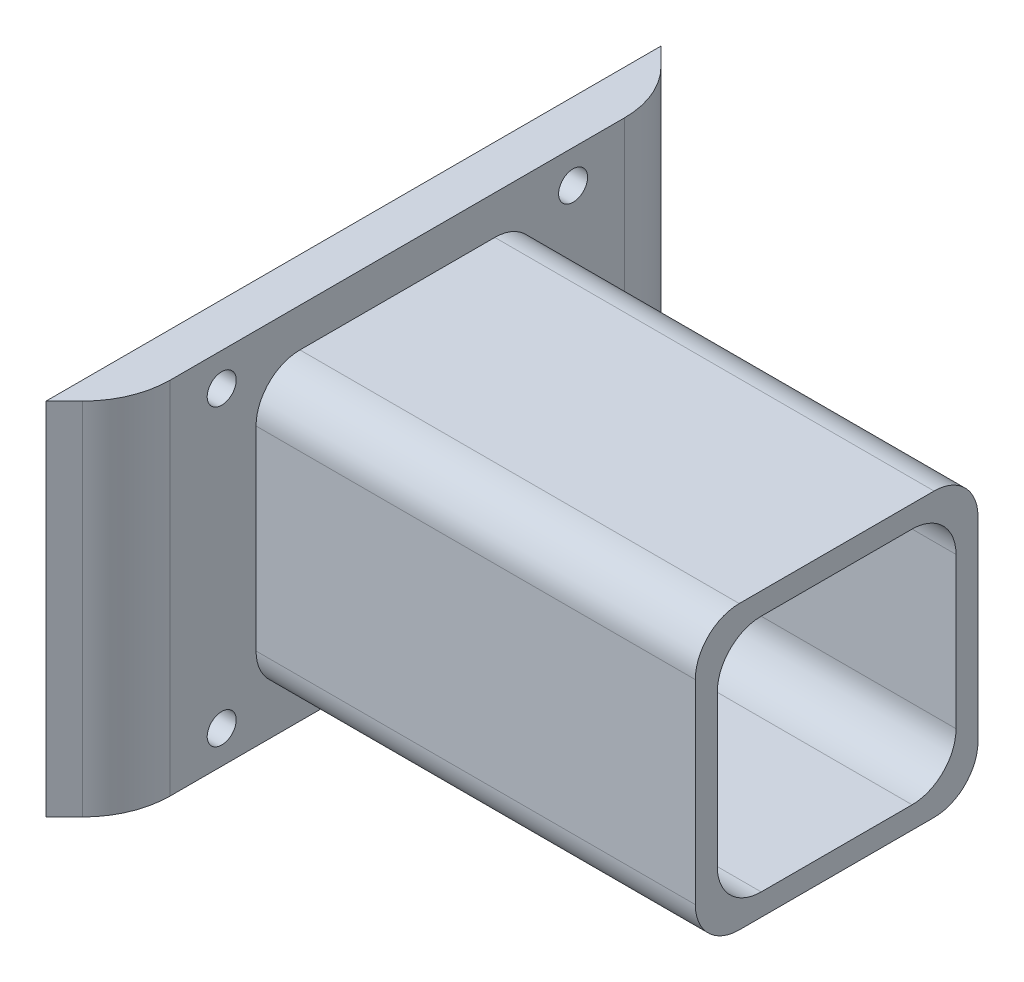
SolidWorks part; units mm, degrees
material "6061 Alloy"
ref_plane "Front Plane" through (0, 0, 0) normal (0, 0, 1) x (1, 0, 0)
ref_plane "Top Plane" through (0, 0, 0) normal (0, 1, 0) x (1, 0, 0)
ref_plane "Right Plane" through (0, 0, 0) normal (1, 0, 0) x (0, 0, -1)
sketch "Sketch1" plane through (0, 0, 0) normal (1, 0, 0) x (0, 0, -1)
  line L1 (-60, -41) -> (60, -41)
  line L2 (-60, -41) -> (-60, 41)
  line L3 (-60, 41) -> (60, 41)
  line L4 (60, -41) -> (60, 41)
  line L5 (-60, -41) -> (60, 41) construction
  line L6 (-60, 41) -> (60, -41) construction
  point P0 (0, 0)
  dimension "D1" = 82
  dimension "D2" = 120
extrude "Boss-Extrude1" add sketch "Sketch1" along normal blind 10
sketch "Sketch6" plane through (0, 41, 0) normal (0, 1, 0) x (1, 0, 0)
  line L0 (0, 60) -> (0, 70)
  line L1 (0, 70) -> (10, 60)
  line L2 (10, 60) -> (0, 60)
  line L3 (0, -60) -> (0, -70)
  line L4 (0, -70) -> (10, -60)
  line L5 (10, -60) -> (0, -60)
  dimension "D1" = 10
  dimension "D2" = 10
extrude "Boss-Extrude4" add sketch "Sketch6" against normal up to surface (82 mm away) up to face at (5, -41, 0)
fillet "Fillet2" radius 20 2 edges at (10, 0, -60) (10, 0, 60)
sketch "Sketch7" plane through (10, 0, 0) normal (1, 0, 0) x (0, 0, -1)
  line L1 (-17.18, -27.18) -> (17.18, -27.18)
  line L2 (-27.18, -17.18) -> (-27.18, 17.18)
  line L3 (-17.18, 27.18) -> (17.18, 27.18)
  line L4 (27.18, -17.18) -> (27.18, 17.18)
  line L5 (-27.18, -27.18) -> (27.18, 27.18) construction
  line L6 (-27.18, 27.18) -> (27.18, -27.18) construction
  line L7 (-22.18, -32.18) -> (22.18, -32.18)
  line L8 (-32.18, -22.18) -> (-32.18, 22.18)
  line L9 (-22.18, 32.18) -> (22.18, 32.18)
  line L10 (32.18, -22.18) -> (32.18, 22.18)
  line L11 (-32.18, -32.18) -> (32.18, 32.18) construction
  line L12 (-32.18, 32.18) -> (32.18, -32.18) construction
  arc A0 (22.18, -32.18) -> (32.18, -22.18) centre (22.18, -22.18) ccw
  arc A1 (22.18, 32.18) -> (32.18, 22.18) centre (22.18, 22.18) cw
  arc A2 (-32.18, 22.18) -> (-22.18, 32.18) centre (-22.18, 22.18) cw
  arc A3 (-22.18, -32.18) -> (-32.18, -22.18) centre (-22.18, -22.18) cw
  arc A4 (-17.18, -27.18) -> (-27.18, -17.18) centre (-17.18, -17.18) cw
  arc A5 (17.18, -27.18) -> (27.18, -17.18) centre (17.18, -17.18) ccw
  arc A6 (17.18, 27.18) -> (27.18, 17.18) centre (17.18, 17.18) cw
  arc A7 (-27.18, 17.18) -> (-17.18, 27.18) centre (-17.18, 17.18) cw
  point P0 (0, 0)
  point P6 (0, 0)
  dimension "D5" = 10
  dimension "D1" = 54.36
  dimension "D2" = 54.36
  dimension "D3" = 5
  dimension "D4" = 5
extrude "Boss-Extrude5" add sketch "Sketch7" along normal blind 100
hole_wizard "M6 Clearance Hole1" positions "Sketch8" profile "Sketch9" hole size "M6" standard "ANSI Metric" end condition up to next
sketch "Sketch8" plane through (10, 0, 0) normal (1, 0, 0) x (0, 0, -1)
  line L0 (51.7157, 41) -> (-51.7157, 41) construction
  line L1 (-51.7157, -41) -> (51.7157, -41) construction
  point P0 (-40, 33.5)
  point P2 (40, 33.5)
  point P4 (40, -33.5)
  point P6 (-40, -33.5)
  dimension "D1" = 7.5
  dimension "D2" = 7.5
  dimension "D3" = 40
  dimension "D4" = 40
sketch "Sketch9" plane through (10, 33.5, 40) normal (0, 1, 0) x (0, 0, -1)
  line L0 (0, 0) -> (0, 10)
  line L1 (0, 10) -> (3.3, 10)
  line L2 (3.3, 10) -> (3.3, 0)
  line L5 (3.3, 0) -> (0, 0)
  line L11 (0, -6.35) -> (0, 107.95) construction
  dimension "Thru Hole Dia." = 6.6
  dimension "Thru Hole Depth" = 10
